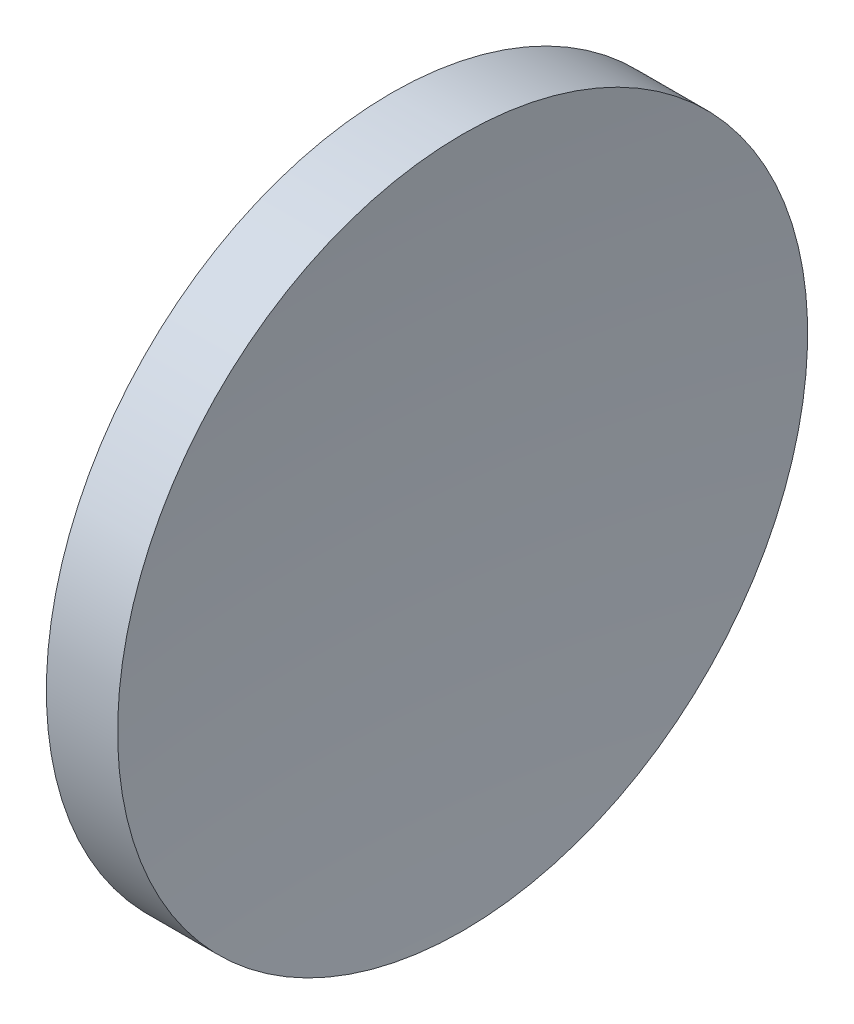
SolidWorks part; units mm, degrees
ref_plane "前视基准面" through (0, 0, 0) normal (0, 0, 1) x (1, 0, 0)
ref_plane "上视基准面" through (0, 0, 0) normal (0, 1, 0) x (1, 0, 0)
ref_plane "右视基准面" through (0, 0, 0) normal (1, 0, 0) x (0, 0, -1)
sketch "草图1" plane through (0, 0, 0) normal (0, 0, 1) x (1, 0, 0)
  line L0 (115.9445, 65.2168) -> (135.9482, 65.2168) construction
  line L1 (124.3832, 77.7168) -> (126.965, 77.7168)
  line L2 (122.6122, 65.2168) -> (126.3122, 65.2168)
  arc A0 (124.3832, 77.7168) -> (122.6122, 65.2168) centre (167.6122, 65.2168) ccw
  arc A1 (126.965, 77.7168) -> (126.3122, 65.2168) centre (246.3122, 65.2168) ccw
revolve "旋转1" add sketch "草图1" angle 360 about L0
